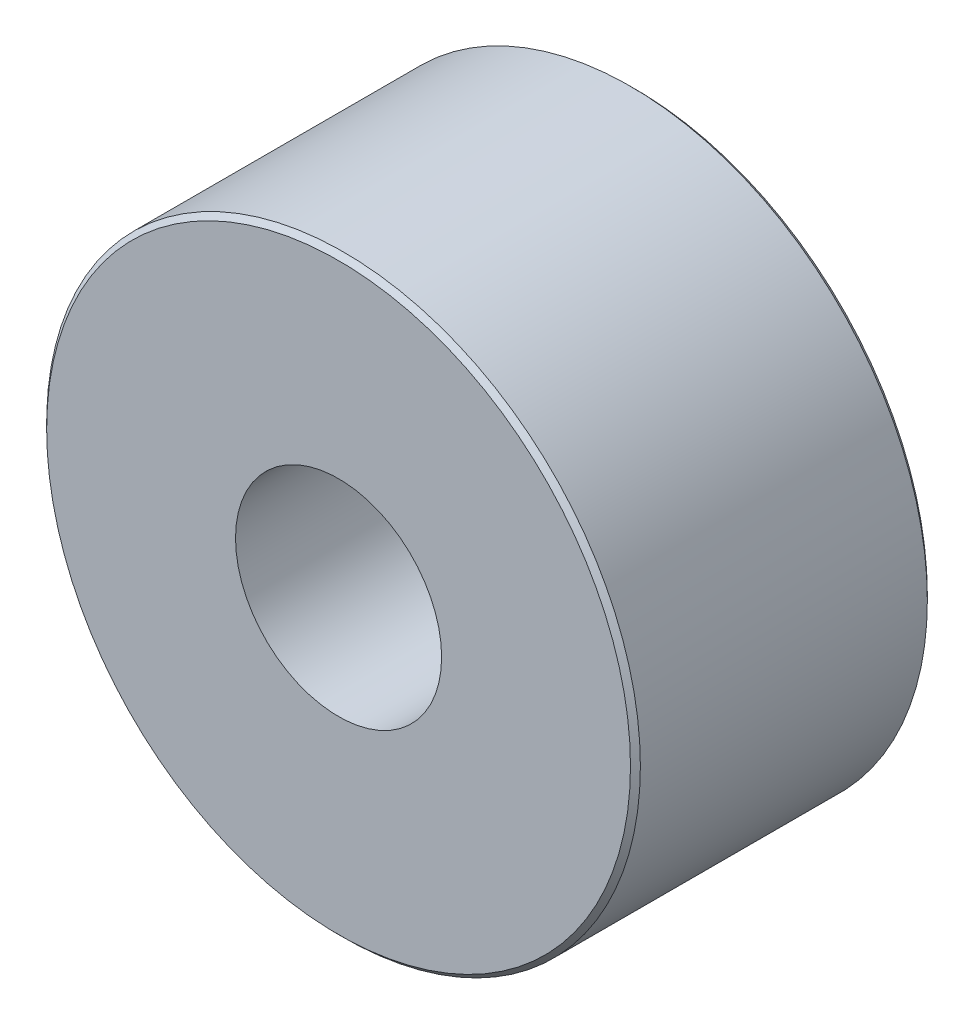
SolidWorks part; units mm, degrees
material "6061-T6 (SS)"
ref_plane "Front" through (0, 0, 0) normal (0, 0, 1) x (1, 0, 0)
ref_plane "Top" through (0, 0, 0) normal (0, 1, 0) x (1, 0, 0)
ref_plane "Right" through (0, 0, 0) normal (1, 0, 0) x (0, 0, -1)
sketch "Sketch1" plane through (0, 0, 0) normal (0, 0, 1) x (1, 0, 0)
  circle A0 centre (0, 0) radius 6
extrude "Boss-Extrude1" add sketch "Sketch1" along normal blind 6
hole_wizard "#8-32 Tapped Hole1" positions "Sketch3" profile "Sketch2" tap size "#8-32" standard "Ansi Inch"
sketch "Sketch3" plane through (0, 0, 6) normal (0, 0, 1) x (1, 0, 0)
  circle A0 centre (0, 0) radius 6 construction
  point P0 (0, 0)
sketch "Sketch2" plane through (0, 0, 6) normal (1, 0, 0) x (0, -1, 0)
  line L0 (0, 0) -> (0, 6.1378)
  line L1 (0, 6.1378) -> (1.7272, 5.1)
  line L2 (1.7272, 5.1) -> (1.7272, 4.2)
  line L3 (1.7272, 4.2) -> (2.0828, 4.2)
  line L4 (2.0828, 4.2) -> (2.0828, 0)
  line L5 (2.0828, 0) -> (0, 0)
  line L10 (0, 6.1378) -> (-1.7272, 5.1) construction
  line L11 (0, -6.35) -> (0, 107.95) construction
  dimension "Tap Drill Dia." = 3.4544
  dimension "Tap Drill Depth" = 5.1
  dimension "Thread Major Dia." = 4.1656
  dimension "Thread Depth" = 4.2
  dimension "Drill Angle" = 118
chamfer "Chamfer1" distance 0.1 angle 45 2 edges at (6, 0, 0) (6, 0, 6)
